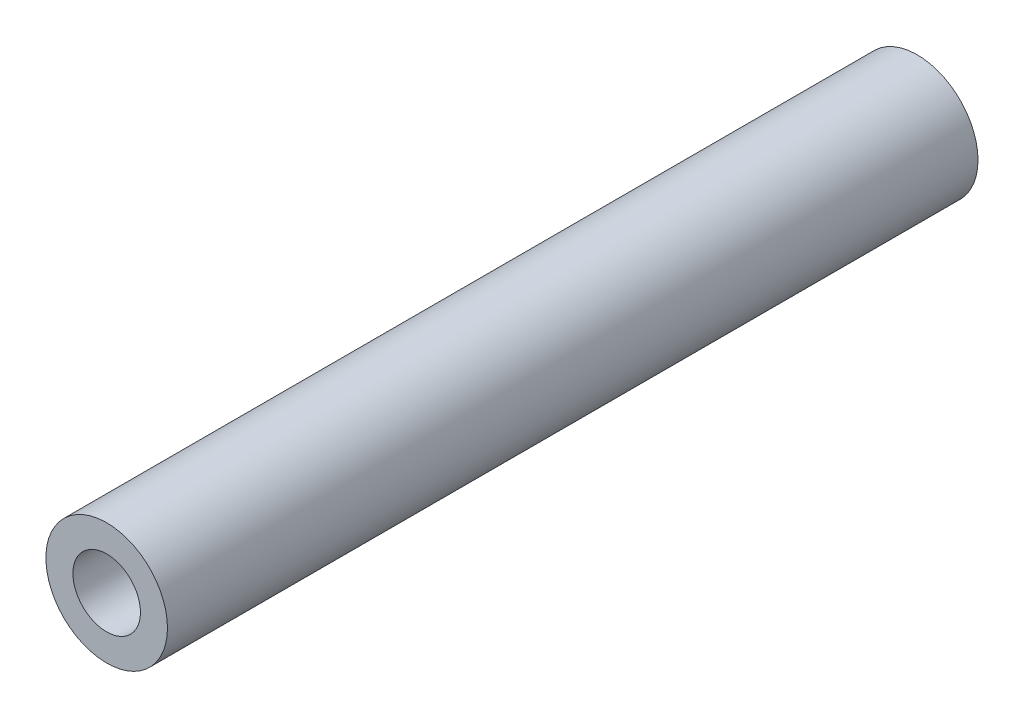
SolidWorks part; units mm, degrees
material "Nylon 101"
ref_plane "Front Plane" through (0, 0, 0) normal (0, 0, 1) x (1, 0, 0)
ref_plane "Top Plane" through (0, 0, 0) normal (0, 1, 0) x (1, 0, 0)
ref_plane "Right Plane" through (0, 0, 0) normal (1, 0, 0) x (0, 0, -1)
sketch "Sketch1" plane through (0, 0, 0) normal (0, 0, 1) x (1, 0, 0)
  circle A0 centre (0, 0) radius 1.5875
  circle A1 centre (0, 0) radius 2.8575
  dimension "D1" = 3.175
  dimension "D2" = 5.715
extrude "Boss-Extrude1" add sketch "Sketch1" along normal blind 38.1
